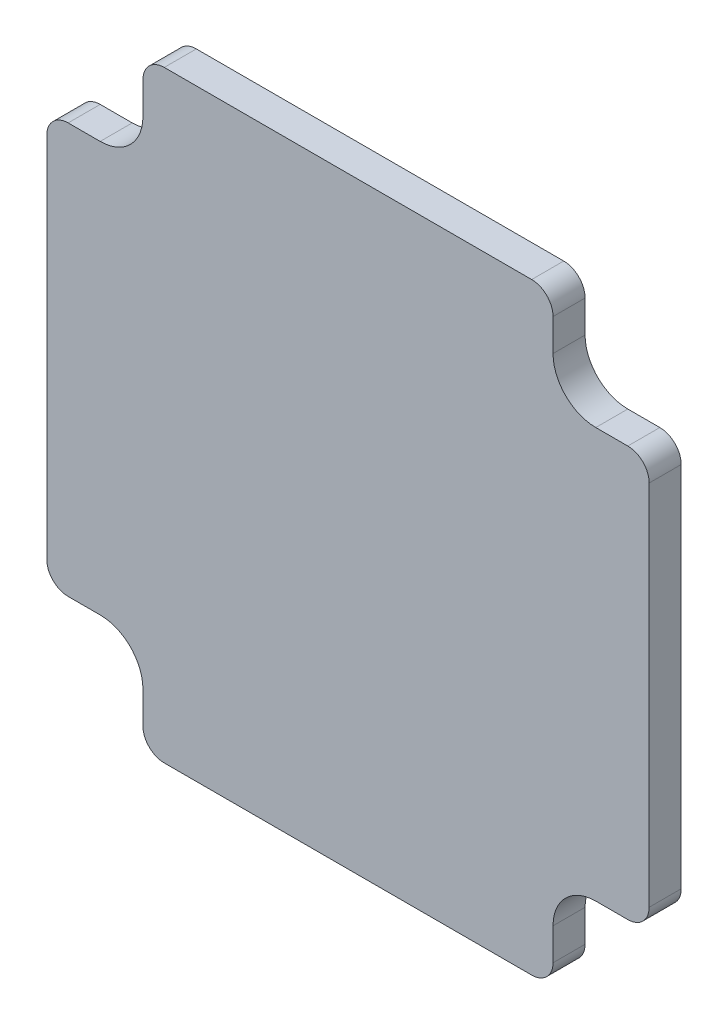
SolidWorks part; units mm, degrees
ref_plane "前视基准面" through (0, 0, 0) normal (0, 0, 1) x (1, 0, 0)
ref_plane "上视基准面" through (0, 0, 0) normal (0, 1, 0) x (1, 0, 0)
ref_plane "右视基准面" through (0, 0, 0) normal (1, 0, 0) x (0, 0, -1)
sketch "草图1" plane through (0, 0, 0) normal (0, 0, 1) x (1, 0, 0)
  line L0 (0, 0) -> (-24.3754, 0) construction
  line B0 (28.2, -17.2) -> (28.2, 17.2)
  line B1 (-28.2, 17.2) -> (-28.2, -17.2)
  line B2 (17.2, 28.2) -> (-17.2, 28.2)
  line B3 (-17.2, -28.2) -> (17.2, -28.2)
  line B4 (-23.2, -19.2) -> (-26.2, -19.2)
  arc B5 (-28.2, -17.2) -> (-26.2, -19.2) centre (-26.2, -17.2) ccw
  arc B6 (-26.2, 19.2) -> (-28.2, 17.2) centre (-26.2, 17.2) ccw
  line B7 (-23.2, 19.2) -> (-26.2, 19.2)
  arc B8 (-23.2, 19.2) -> (-19.2, 23.2) centre (-23.2, 23.2) ccw
  line B9 (-19.2, 26.2) -> (-19.2, 23.2)
  arc B10 (-17.2, 28.2) -> (-19.2, 26.2) centre (-17.2, 26.2) ccw
  arc B11 (19.2, 26.2) -> (17.2, 28.2) centre (17.2, 26.2) ccw
  line B12 (19.2, 26.2) -> (19.2, 23.2)
  arc B13 (19.2, 23.2) -> (23.2, 19.2) centre (23.2, 23.2) ccw
  line B14 (23.2, 19.2) -> (26.2, 19.2)
  arc B15 (28.2, 17.2) -> (26.2, 19.2) centre (26.2, 17.2) ccw
  arc B16 (26.2, -19.2) -> (28.2, -17.2) centre (26.2, -17.2) ccw
  line B17 (23.2, -19.2) -> (26.2, -19.2)
  arc B18 (23.2, -19.2) -> (19.2, -23.2) centre (23.2, -23.2) ccw
  line B19 (19.2, -26.2) -> (19.2, -23.2)
  arc B20 (17.2, -28.2) -> (19.2, -26.2) centre (17.2, -26.2) ccw
  arc B21 (-19.2, -26.2) -> (-17.2, -28.2) centre (-17.2, -26.2) ccw
  line B22 (-19.2, -26.2) -> (-19.2, -23.2)
  arc B23 (-19.2, -23.2) -> (-23.2, -19.2) centre (-23.2, -23.2) ccw
sketch_block_instance "MotorControlBoad-1"
sketch_block "MotorControlBoad" parameters "D1"=32.9726, "D2"=24.7505, "D3"=24.3754
extrude "凸台-拉伸1" add sketch "草图1" along normal blind 3
sketch "草图2" plane through (0, 0, 3) normal (0, 0, 1) x (1, 0, 0)
  line L1 (15.75, 25.5) -> (-15.75, 25.5) construction
  line L2 (15.75, 25.5) -> (15.75, -25.5) construction
  line L3 (15.75, -25.5) -> (-15.75, -25.5) construction
  line L4 (-15.75, 25.5) -> (-15.75, -25.5) construction
  line L5 (15.75, 25.5) -> (-15.75, -25.5) construction
  line L6 (15.75, -25.5) -> (-15.75, 25.5) construction
  circle A0 centre (-15.75, -25.5) radius 1.65
  circle A2 centre (15.75, -25.5) radius 1.65
  circle A3 centre (15.75, 25.5) radius 1.65
  circle A4 centre (-15.75, 25.5) radius 1.65
  circle A5 centre (-15.75, -25.5) radius 2.5
  point P2 (0, 0)
  dimension "D1" = 3.3
  dimension "D2" = 5
  dimension "D3" = 25.5
  dimension "D4" = 15.75
